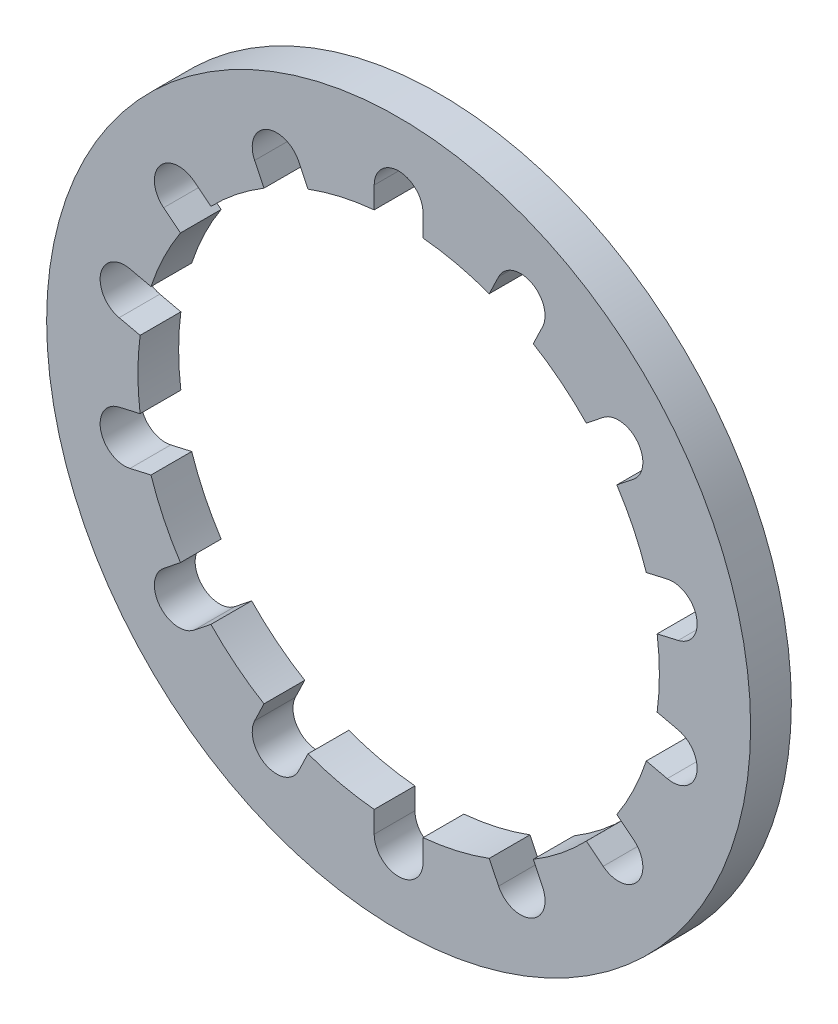
SolidWorks part; units mm, degrees
ref_plane "Front" through (0, 0, 0) normal (0, 0, 1) x (1, 0, 0)
ref_plane "Top" through (0, 0, 0) normal (0, 1, 0) x (1, 0, 0)
ref_plane "Right" through (0, 0, 0) normal (1, 0, 0) x (0, 0, -1)
sketch "Sketch1" plane through (0, 0, 0) normal (0, 0, 1) x (1, 0, 0)
  circle A0 centre (0, 0) radius 5.4864
  dimension "D1" = 10.9728
extrude "Base-Extrude" add sketch "Sketch1" along normal blind 0.635
sketch "Sketch2" plane through (0, 0, 0.635) normal (0, 0, 1) x (1, 0, 0)
  circle A0 centre (0, 0) radius 4.064
  dimension "D1" = 8.128
extrude "Cut-Extrude1" cut sketch "Sketch2" against normal through all
sketch "Sketch3" plane through (0, 0, 0.635) normal (0, 0, 1) x (1, 0, 0)
  line L0 (0, 6.2104) -> (0, -6.2104) construction
  line L1 (0.381, 4.0461) -> (0.381, 4.3815)
  line L2 (-0.381, 4.0461) -> (-0.381, 4.3815)
  circle A0 centre (0, 0) radius 4.064 construction
  arc A1 (0.381, 4.3815) -> (-0.381, 4.3815) centre (0, 4.3815) ccw
  arc A2 (0.381, 4.0461) -> (-0.381, 4.0461) centre (0, 0) ccw
  point P2 (0, 0)
  dimension "D2" = 0.381
  dimension "D1" = 4.7625
extrude "Cut-Extrude4" cut sketch "Sketch3" against normal through all
pattern_circular "CirPattern1" count 14 over 360 about axis through (0, 0, 0) along (0, 0, 1) of "Cut-Extrude4"
